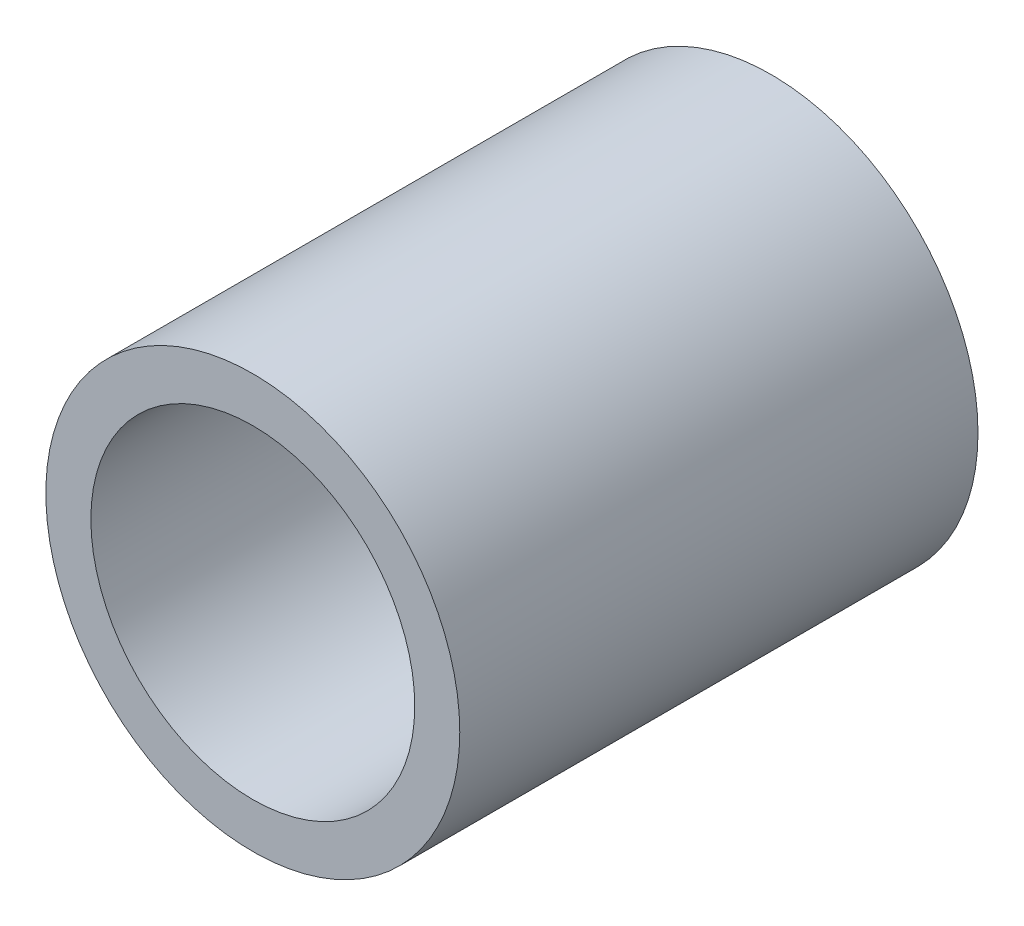
SolidWorks part; units mm, degrees
ref_plane "Front Plane" through (0, 0, 0) normal (0, 0, 1) x (1, 0, 0)
ref_plane "Top Plane" through (0, 0, 0) normal (0, 1, 0) x (1, 0, 0)
ref_plane "Right Plane" through (0, 0, 0) normal (1, 0, 0) x (0, 0, -1)
sketch "Sketch1" plane through (0, 0, 0) normal (0, 0, 1) x (1, 0, 0)
  circle A0 centre (-7.4735, 0) radius 15.975
  circle A1 centre (-7.4735, 0) radius 12.5
extrude "Boss-Extrude1" add sketch "Sketch1" along normal blind 40
